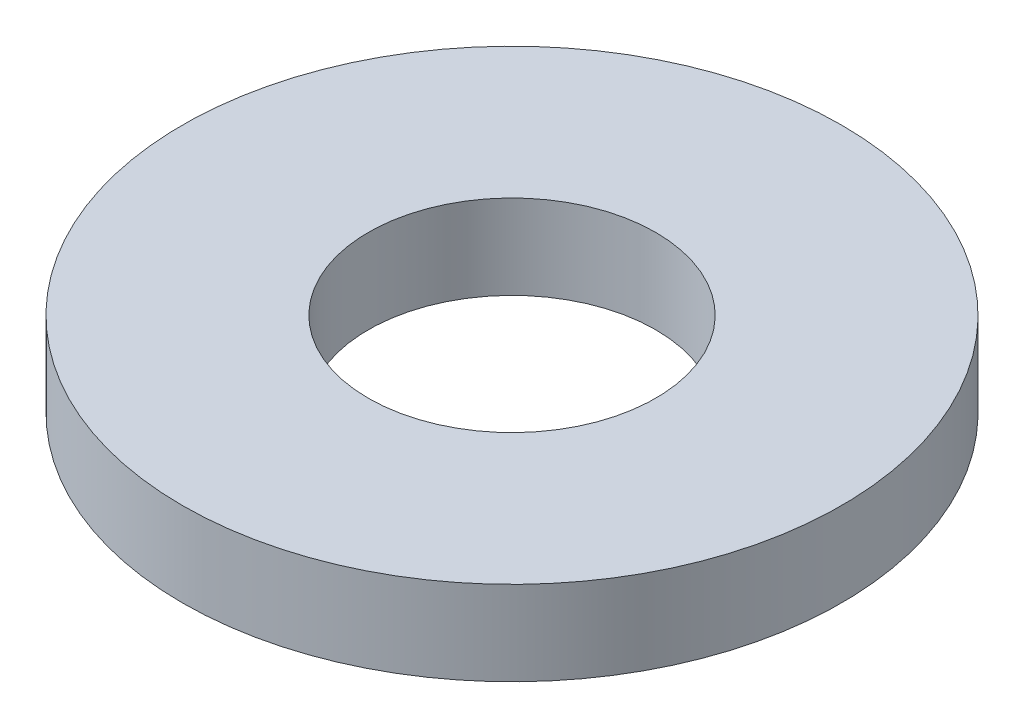
SolidWorks part; units mm, degrees
ref_plane "Front Plane" through (0, 0, 0) normal (0, 0, 1) x (1, 0, 0)
ref_plane "Top Plane" through (0, 0, 0) normal (0, 1, 0) x (1, 0, 0)
ref_plane "Right Plane" through (0, 0, 0) normal (1, 0, 0) x (0, 0, -1)
sketch "Sketch1" plane through (0, 0, 0) normal (0, 1, 0) x (1, 0, 0)
  circle A0 centre (0, 0) radius 3.175
  dimension "OD" = 6.35
extrude "Boss-Extrude1" add sketch "Sketch1" along normal blind 0.8128
sketch "Sketch5" plane through (0, 0.8128, 0) normal (0, 1, 0) x (-1, 0, 0)
  circle A0 centre (0, 0) radius 1.3843
  dimension "ID" = 2.7686
extrude "Cut-Extrude1" cut sketch "Sketch5" against normal through all
